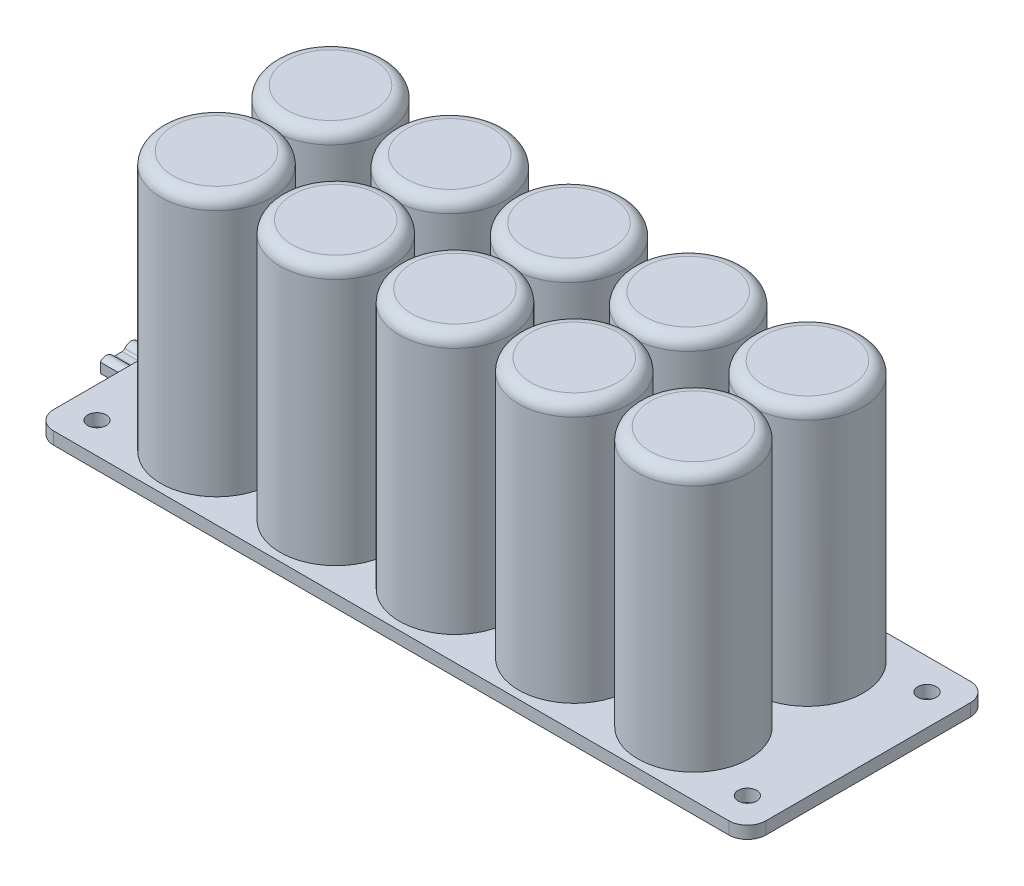
SolidWorks part; units mm, degrees
ref_plane "前视基准面" through (0, 0, 0) normal (0, 0, 1) x (1, 0, 0)
ref_plane "上视基准面" through (0, 0, 0) normal (0, 1, 0) x (1, 0, 0)
ref_plane "右视基准面" through (0, 0, 0) normal (1, 0, 0) x (0, 0, -1)
sketch "草图1" plane through (0, 0, 0) normal (0, 1, 0) x (1, 0, 0)
  line L1 (-54.5, 19.5) -> (54.5, 19.5)
  line L2 (-57.5, 16.5) -> (-57.5, -16.5)
  line L3 (-54.5, -19.5) -> (54.5, -19.5)
  line L4 (57.5, 16.5) -> (57.5, -16.5)
  line L5 (0, -19.5) -> (0, 19.5) construction
  line L6 (-57.5, 0) -> (57.5, 0) construction
  arc A0 (54.5, 19.5) -> (57.5, 16.5) centre (54.5, 16.5) cw
  arc A1 (54.5, -19.5) -> (57.5, -16.5) centre (54.5, -16.5) ccw
  arc A2 (-54.5, 19.5) -> (-57.5, 16.5) centre (-54.5, 16.5) ccw
  arc A3 (-57.5, -16.5) -> (-54.5, -19.5) centre (-54.5, -16.5) ccw
  point P0 (0, 0)
  point P6 (57.5, 19.5)
  point P14 (-57.5, 19.5)
  point P17 (-57.5, -19.5)
  dimension "D3" = 3
  dimension "D1" = 115
  dimension "D2" = 39
extrude "凸台-拉伸1" add sketch "草图1" along normal blind 2
sketch "草图2" plane through (0, 2, 0) normal (0, 1, 0) x (1, 0, 0)
  line L0 (-57.5, 0) -> (57.5, 0) construction
  line L1 (-57.5, 16.5) -> (-57.5, -16.5) construction
  line L2 (57.5, -16.5) -> (57.5, 16.5) construction
  line L3 (0, 19.5) -> (0, -19.5) construction
  line L4 (54.5, 19.5) -> (-54.5, 19.5) construction
  circle A0 centre (0, 9.2) radius 9
  circle A1 centre (-19.25, 9.2) radius 9
  circle A2 centre (-38.5, 9.2) radius 9
  circle A3 centre (19.25, 9.2) radius 9
  circle A4 centre (38.5, 9.2) radius 9
  circle A5 centre (38.5, -9.2) radius 9
  circle A6 centre (19.25, -9.2) radius 9
  circle A7 centre (-38.5, -9.2) radius 9
  circle A8 centre (-19.25, -9.2) radius 9
  circle A9 centre (0, -9.2) radius 9
  point P23 (0, 0)
  dimension "D1" = 18
  dimension "D4" = 19.25
  dimension "D5" = 19.25
  dimension "D6" = 18.4
  dimension "D2" = 3
  dimension "D3" = 3
extrude "凸台-拉伸3" add sketch "草图2" along normal blind 42
fillet "圆角1" radius 2 10 edges at (-38.5, 44, -0.2) (-19.25, 44, -0.2) (0, 44, -0.2) (19.25, 44, -0.2) (38.5, 44, -0.2) (38.5, 44, 0.2) (19.25, 44, 0.2) (0, 44, 0.2) (-19.25, 44, 0.2) (-38.5, 44, 0.2)
sketch "草图4" plane through (0, 0, 0) normal (0, -1, 0) x (1, 0, 0)
  line L0 (57.5, 0) -> (-63.8615, 0) construction
  line L1 (57.5, 16.5) -> (57.5, -16.5) construction
  line L2 (0, -19.5) -> (0, 19.5) construction
  line L3 (54.5, -19.5) -> (-54.5, -19.5) construction
  line L4 (-54.5, 19.5) -> (54.5, 19.5) construction
  circle A0 centre (-52.5, 14.5) radius 1.5
  circle A1 centre (-52.5, -14.5) radius 1.5
  circle A2 centre (52.5, -14.5) radius 1.5
  circle A3 centre (52.5, 14.5) radius 1.5
  dimension "D1" = 3
  dimension "D3" = 105
  dimension "D2" = 29
extrude "切除-拉伸1" cut sketch "草图4" against normal through all
sketch "草图5" plane through (-57.5, 0, 0) normal (-1, 0, 0) x (0, 0, 1)
  line L0 (-6.5, 0) -> (6.5, 0)
  line L1 (-16.5, 0) -> (16.5, 0) construction
  line L2 (6.5, 0) -> (6.5, -3.85)
  line L3 (6.5, -3.85) -> (-6.5, -3.85)
  line L4 (-6.5, -3.85) -> (-6.5, 0)
  line L5 (0, 2) -> (0, -10.5365) construction
  line L6 (-16.5, 2) -> (16.5, 2) construction
  dimension "D1" = 13
  dimension "D2" = 3.85
extrude "凸台-拉伸4" add sketch "草图5" against normal blind 10
sketch "草图6" plane through (-57.5, 0, 0) normal (-1, 0, 0) x (0, 0, 1)
  line L0 (-6.5, -1.925) -> (6.5, -1.925) construction
  line L1 (-6.5, 0) -> (-6.5, -3.85) construction
  line L2 (6.5, -3.85) -> (6.5, 0) construction
  line L3 (0, -3.85) -> (0, 2) construction
  line L4 (-6.5, -3.85) -> (6.5, -3.85) construction
  line L5 (-16.5, 2) -> (16.5, 2) construction
  line L6 (-0.5639, -1.425) -> (0.5639, -1.425)
  line L9 (-0.5639, -2.425) -> (0.5639, -2.425)
  line L10 (2.9711, -1.1379) -> (2.9711, -2.7121)
  circle A0 centre (-2, -1.925) radius 0.75
  circle A1 centre (2, -1.925) radius 0.75
  arc A2 (-0.9742, -1.2107) -> (-0.9742, -2.6393) centre (-2, -1.925) ccw
  arc A3 (0.9742, -2.6393) -> (2.9711, -2.7121) centre (2, -1.925) ccw
  arc A6 (0.5639, -1.425) -> (0.9742, -1.2107) centre (0.5639, -0.925) ccw
  arc A7 (0.5639, -2.425) -> (0.9742, -2.6393) centre (0.5639, -2.925) cw
  arc A8 (-0.5639, -2.425) -> (-0.9742, -2.6393) centre (-0.5639, -2.925) ccw
  arc A9 (-0.5639, -1.425) -> (-0.9742, -1.2107) centre (-0.5639, -0.925) cw
  arc A10 (2.9711, -1.1379) -> (0.9742, -1.2107) centre (2, -1.925) ccw
  dimension "D1" = 1.5
  dimension "D2" = 2.5
  dimension "D5" = 0.5
  dimension "D3" = 1
  dimension "D4" = 2
extrude "凸台-拉伸5" add sketch "草图6" along normal blind 6
